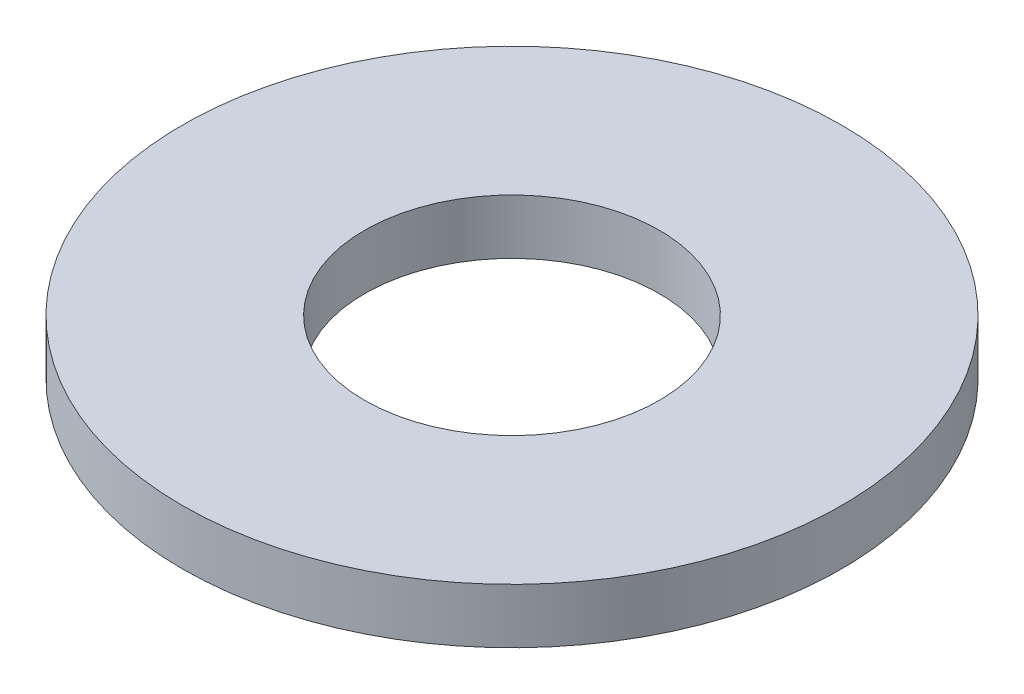
SolidWorks part; units mm, degrees
ref_plane "Front Plane" through (0, 0, 0) normal (0, 0, 1) x (1, 0, 0)
ref_plane "Top Plane" through (0, 0, 0) normal (0, 1, 0) x (1, 0, 0)
ref_plane "Right Plane" through (0, 0, 0) normal (1, 0, 0) x (0, 0, -1)
sketch "Sketch1" plane through (0, 0, 0) normal (0, 1, 0) x (1, 0, 0)
  circle A0 centre (0, 0) radius 4.025
  circle A1 centre (0, 0) radius 9
  dimension "D1" = 8.05
  dimension "D2" = 18
extrude "Boss-Extrude1" add sketch "Sketch1" along normal blind 1.5
